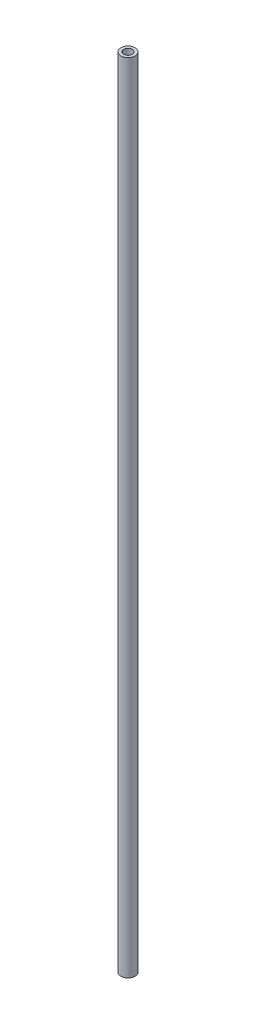
SolidWorks part; units mm, degrees
material "Thornel VCB-20 Carbon Cloth"
ref_plane "Front Plane" through (0, 0, 0) normal (0, 0, 1) x (1, 0, 0)
ref_plane "Top Plane" through (0, 0, 0) normal (0, 1, 0) x (1, 0, 0)
ref_plane "Right Plane" through (0, 0, 0) normal (1, 0, 0) x (0, 0, -1)
sketch "Sketch2" plane through (0, 0, 0) normal (0, 1, 0) x (1, 0, 0)
  circle A0 centre (0, 0) radius 2.5
  circle A1 centre (0, 0) radius 1.5
  dimension "D1" = 5
  dimension "D2" = 3
extrude "Boss-Extrude3" add sketch "Sketch2" along normal mid plane 280 contours A1 | A0
